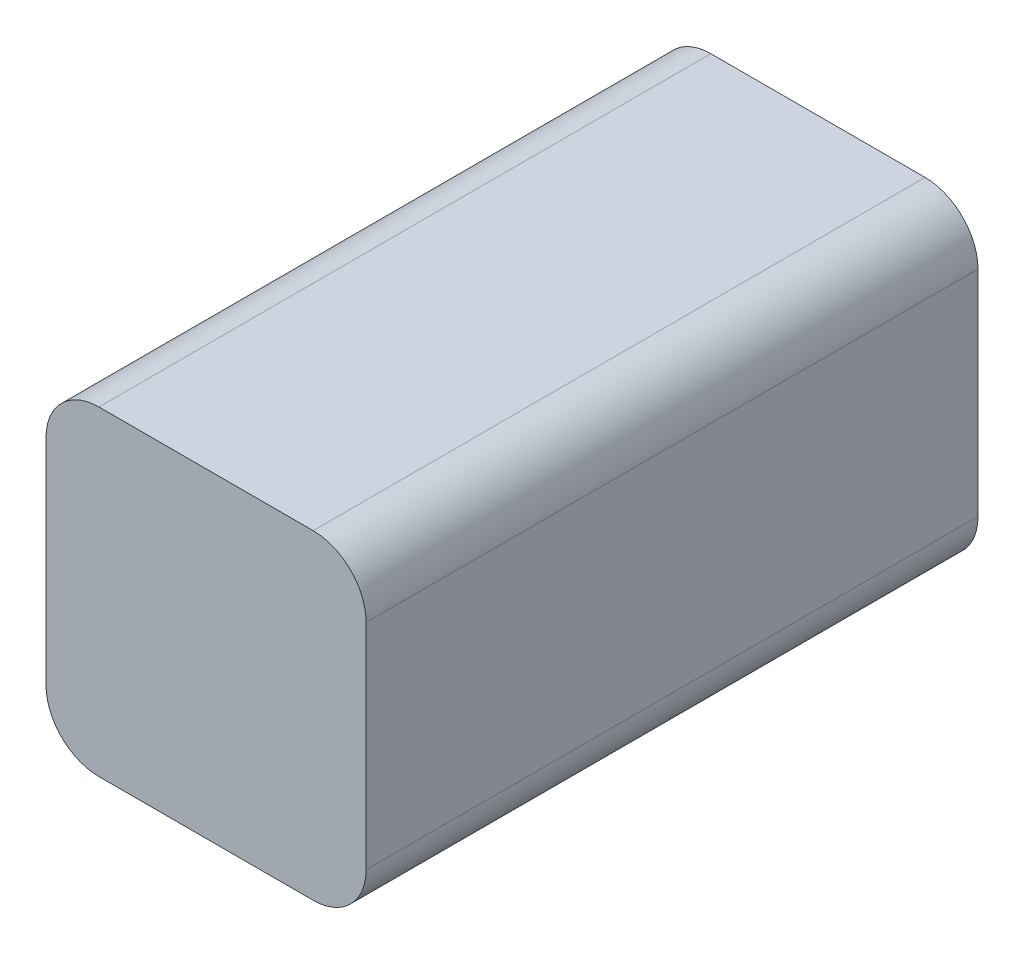
SolidWorks part; units mm, degrees
ref_plane "Front Plane" through (0, 0, 0) normal (0, 0, 1) x (1, 0, 0)
ref_plane "Top Plane" through (0, 0, 0) normal (0, 1, 0) x (1, 0, 0)
ref_plane "Right Plane" through (0, 0, 0) normal (1, 0, 0) x (0, 0, -1)
ref_plane "Plane1" through (0, -4, 0) normal (0, -1, 0) x (1, 0, 0)
sketch "Sketch1" plane through (0, -4, 0) normal (0, -1, 0) x (1, 0, 0)
  line L0 (15.2, 21.7) -> (-4, 21.7)
  line L1 (-4, 21.7) -> (-4, -15)
  line L2 (-4, -15) -> (15.2, -15)
  line L3 (15.2, -15) -> (15.2, 21.7)
extrude "Boss-Extrude1" add sketch "Sketch1" against normal blind 19.2
sketch "Sketch2" plane through (0, 0, -15) normal (0, 0, -1) x (-1, 0, 0)
  line L0 (-11.5, -0.3) -> (0.3, -0.3)
  line L1 (0.3, -0.3) -> (0.3, 11.5)
  line L2 (0.3, 11.5) -> (-11.5, 11.5)
  line L3 (-11.5, 11.5) -> (-11.5, -0.3)
extrude "Cut-Extrude1" cut sketch "Sketch2" against normal blind 34.2
fillet "Fillet1" radius 3.175 4 edges at (15.2, 15.2, 3.35) (15.2, -4, 3.35) (-4, 15.2, 3.35) (-4, -4, 3.35)
